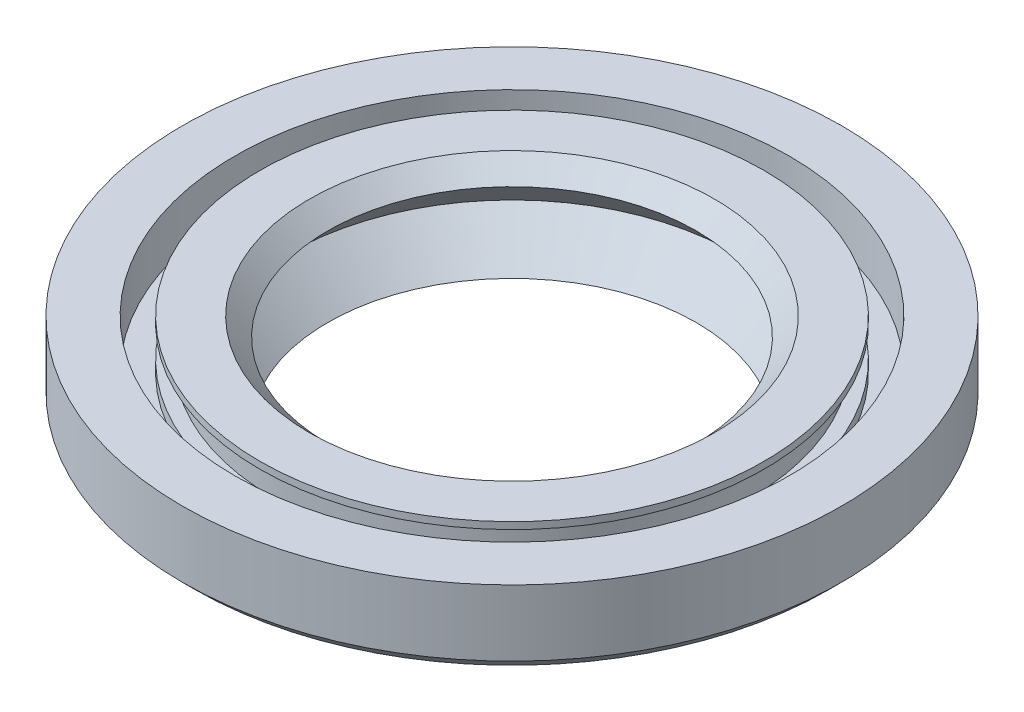
SolidWorks part; units mm, degrees
ref_plane "Спереди" through (0, 0, 0) normal (0, 0, 1) x (1, 0, 0)
ref_plane "Сверху" through (0, 0, 0) normal (0, 1, 0) x (1, 0, 0)
ref_plane "Справа" through (0, 0, 0) normal (1, 0, 0) x (0, 0, -1)
sketch "Эскиз1" plane through (0, 0, 0) normal (0, 0, 1) x (1, 0, 0)
  line L0 (11.526, -1.2213) -> (9.5, 0.8047)
  line L1 (9.5, 0.8047) -> (10.4456, 1.7503)
  line L2 (10.4456, 1.7503) -> (13, 1.7503)
  line L3 (13, 1.7503) -> (13, 1.3959)
  line L4 (11.9993, -3.5931) -> (14.071, -2.2838)
  line L5 (14.2944, -0.7851) -> (14.2944, 1.7503)
  line L6 (14.2944, 1.7503) -> (17, 1.7503)
  line L7 (17, 1.7503) -> (17, -1.6544)
  line L8 (17, -1.6544) -> (16.3706, -2.2838)
  line L9 (16.3706, -2.2838) -> (14.071, -2.2838)
  line L10 (13, -0.2083) -> (13, -0.7851)
  line L11 (13, -0.7851) -> (14.2944, -0.7851)
  line L12 (13, 1.3959) -> (12.3165, 1.3959)
  line L13 (11.9993, -3.5931) -> (9.5, -3.2932)
  line L14 (9.5, -3.2932) -> (11.526, -1.2213)
  line L15 (0, 17.2088) -> (0, -18.0622) construction
  line L16 (12.3165, 1.3959) -> (12.3165, -0.2083)
  line L17 (12.3165, -0.2083) -> (13, -0.2083)
  dimension "D1" = 9.5
  dimension "D2" = 17
revolve "Повернуть1" add sketch "Эскиз1" angle 360 about L15
